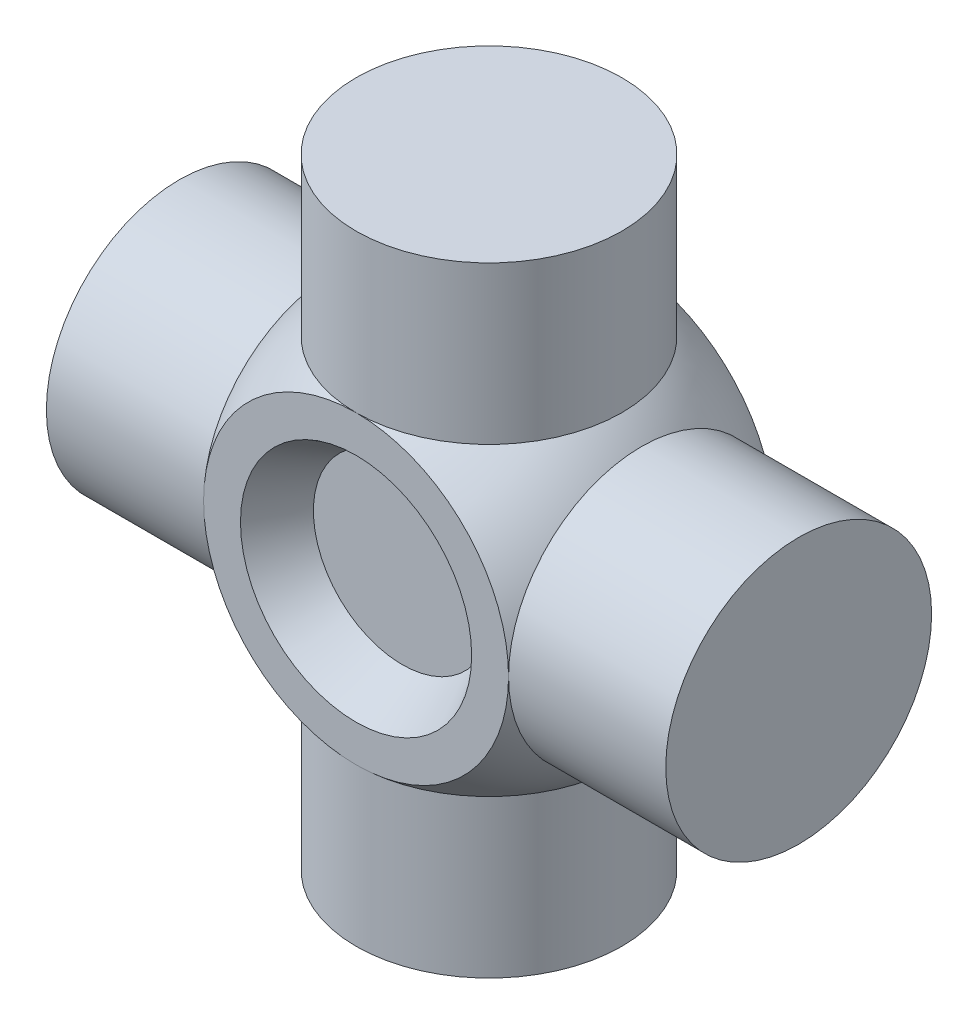
SolidWorks part; units mm, degrees
material "Alloy Steel"
ref_plane "Front Plane" through (0, 0, 0) normal (0, 0, 1) x (1, 0, 0)
ref_plane "Top Plane" through (0, 0, 0) normal (0, 1, 0) x (1, 0, 0)
ref_plane "Right Plane" through (0, 0, 0) normal (1, 0, 0) x (0, 0, -1)
sketch "Sketch1" plane through (0, 0, 0) normal (0, 1, 0) x (1, 0, 0)
  line L0 (0, -7.8368) -> (0, 8.361) construction
  line L1 (0, 11.1125) -> (0, -11.1125)
  arc A0 (0, -11.1125) -> (0, 11.1125) centre (0, 0) ccw
  dimension "D1" = 22.225
revolve "Revolve1" add sketch "Sketch1" angle 360 about L0
sketch "Sketch2" plane through (0, 0, 0) normal (0, 1, 0) x (1, 0, 0)
  line L0 (-8.3762, 7.3025) -> (8.3762, 7.3025)
  line L1 (-5.4395, 0) -> (6.9325, 0) construction
  line L2 (8.3762, 7.3025) -> (8.3762, -7.3025)
  line L3 (-8.3762, 7.3025) -> (-8.3762, -7.3025)
  line L4 (-8.3762, -7.3025) -> (8.3762, -7.3025)
  circle A0 centre (0, 0) radius 11.1125 construction
  point P2 (0, 7.3025)
  point P12 (8.3762, 0)
  point P13 (-8.3762, 0)
  dimension "D1" = 16.7525
  dimension "D2" = 7.3025
extrude "Cut-Extrude1" cut sketch "Sketch2" against normal mid plane 20.574 flip side to cut
sketch "Sketch3" plane through (0, 0, 0) normal (1, 0, 0) x (0, 0, -1)
  line L0 (-7.3025, 8.3762) -> (7.3025, 8.3762)
  line L1 (-5.6768, 0) -> (8.2461, 0) construction
  line L2 (7.3025, 8.3762) -> (7.3025, -8.3762)
  line L3 (-7.3025, 8.3762) -> (-7.3025, -8.3762)
  line L4 (-7.3025, -8.3762) -> (7.3025, -8.3762)
  arc A0 (7.3025, 8.3762) -> (-7.3025, 8.3762) centre (0, 0) ccw construction
  point P3 (0, 8.3762)
  point P9 (-4.7625, 0)
  point P10 (4.7625, 0)
  point P14 (7.3025, 0)
  point P15 (-7.3025, 0)
extrude "Cut-Extrude3" cut sketch "Sketch3" against normal mid plane 22.606 flip side to cut
sketch "Sketch6" plane through (0, 0, 7.3025) normal (0, 0, 1) x (1, 0, 0)
  circle A0 centre (0, 0) radius 6.35
  dimension "D1" = 12.7
extrude "Cut-Extrude4" cut sketch "Sketch6" against normal blind 2.54 draft 30
mirror "Mirror1" about plane through (0, 0, 0) normal (0, 0, 1) of "Cut-Extrude4"
sketch "Sketch7" plane through (8.3762, 0, 0) normal (1, 0, 0) x (0, 0, -1)
  arc A2 (7.3025, 0) -> (-7.3025, 0) centre (0, 0) ccw
  arc A3 (7.3025, 0) -> (-7.3025, 0) centre (0, 0) ccw
  arc A4 (-7.3025, 0) -> (7.3025, 0) centre (0, 0) ccw
  arc A5 (-7.3025, 0) -> (7.3025, 0) centre (0, 0) ccw
  dimension "D1" = 0
extrude "Boss-Extrude1" add sketch "Sketch7" along normal blind 8.636
sketch "Sketch11" plane through (0, 8.3762, 0) normal (0, 1, 0) x (1, 0, 0)
  arc A2 (0, -7.3025) -> (0, 7.3025) centre (0, 0) ccw
  arc A3 (0, 7.3025) -> (0, -7.3025) centre (0, 0) ccw
  arc A4 (0, -7.3025) -> (0, 7.3025) centre (0, 0) ccw
  arc A5 (0, 7.3025) -> (0, -7.3025) centre (0, 0) ccw
  dimension "D1" = 0
extrude "Boss-Extrude2" add sketch "Sketch11" along normal blind 8.636
sketch "Sketch12" plane through (-8.3762, 0, 0) normal (-1, 0, 0) x (0, 0, 1)
  arc A2 (7.3025, 0) -> (-7.3025, 0) centre (0, 0) ccw
  arc A3 (-7.3025, 0) -> (7.3025, 0) centre (0, 0) ccw
  arc A4 (7.3025, 0) -> (-7.3025, 0) centre (0, 0) ccw
  arc A5 (-7.3025, 0) -> (7.3025, 0) centre (0, 0) ccw
  dimension "D1" = 0
extrude "Boss-Extrude3" add sketch "Sketch12" along normal blind 8.636
sketch "Sketch13" plane through (0, -8.3762, 0) normal (0, -1, 0) x (1, 0, 0)
  arc A2 (0, -7.3025) -> (0, 7.3025) centre (0, 0) ccw
  arc A3 (0, 7.3025) -> (0, -7.3025) centre (0, 0) ccw
  arc A4 (0, -7.3025) -> (0, 7.3025) centre (0, 0) ccw
  arc A5 (0, 7.3025) -> (0, -7.3025) centre (0, 0) ccw
  dimension "D1" = 0
extrude "Boss-Extrude4" add sketch "Sketch13" along normal blind 8.636
